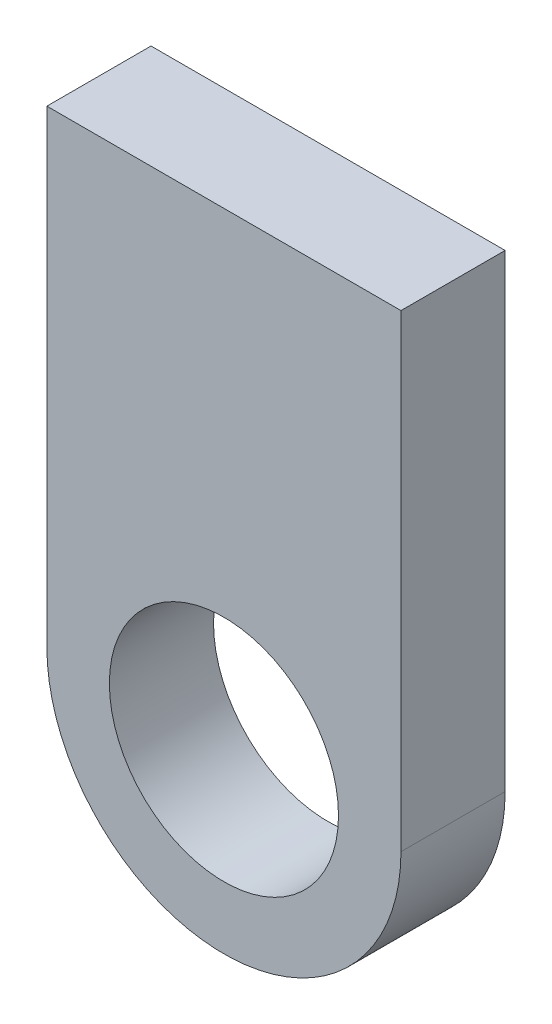
SolidWorks part; units mm, degrees
ref_plane "Front Plane" through (0, 0, 0) normal (0, 0, 1) x (1, 0, 0)
ref_plane "Top Plane" through (0, 0, 0) normal (0, 1, 0) x (1, 0, 0)
ref_plane "Right Plane" through (0, 0, 0) normal (1, 0, 0) x (0, 0, -1)
sketch "Sketch2" plane through (0, 0, 0) normal (0, 0, 1) x (1, 0, 0)
  line L0 (-0.85, 0) -> (0.85, 0) construction
  line L1 (-0.85, 2.25) -> (0.85, 2.25)
  line L2 (-0.85, 2.25) -> (-0.85, 0)
  line L4 (0.85, 2.25) -> (0.85, 0)
  arc A0 (-0.85, 0) -> (0.85, 0) centre (0, 0) ccw
  circle A1 centre (0, 0) radius 0.55
  point P4 (0, 0)
  dimension "D3" = 1.1
  dimension "D4" = 0.85
  dimension "D1" = 1.7
  dimension "D2" = 2.25
extrude "Boss-Extrude1" add sketch "Sketch2" along normal blind 0.5
